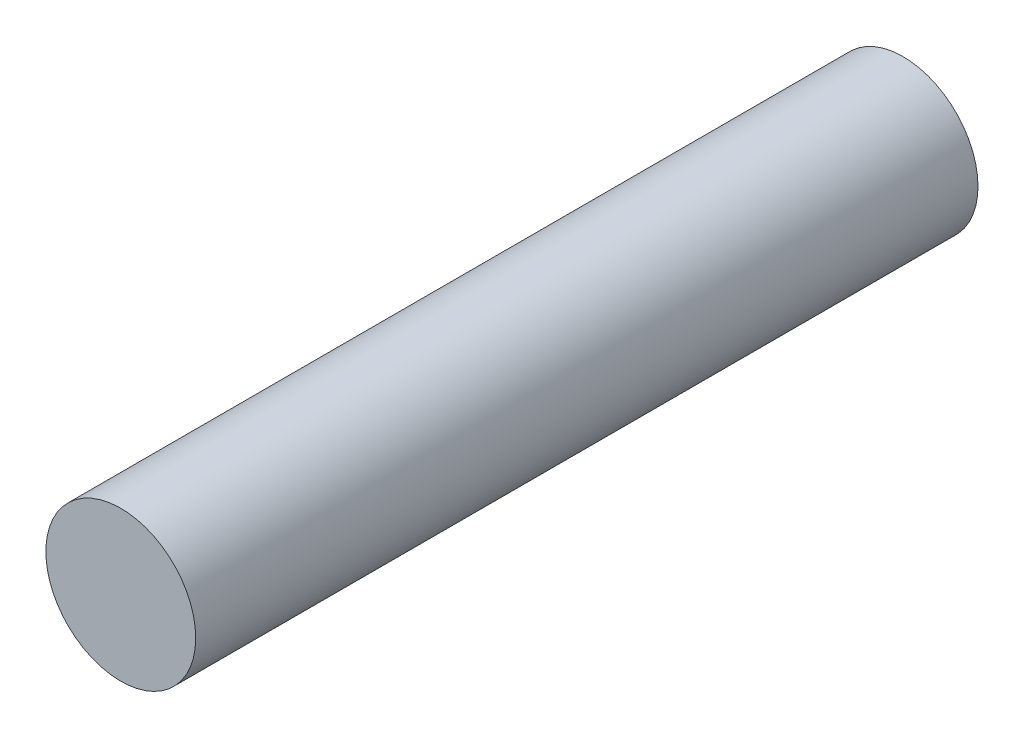
SolidWorks part; units mm, degrees
ref_plane "Front Plane" through (0, 0, 0) normal (0, 0, 1) x (1, 0, 0)
ref_plane "Top Plane" through (0, 0, 0) normal (0, 1, 0) x (1, 0, 0)
ref_plane "Right Plane" through (0, 0, 0) normal (1, 0, 0) x (0, 0, -1)
sketch "Sketch1" plane through (0, 0, 0) normal (0, 0, 1) x (1, 0, 0)
  circle A0 centre (0, 0) radius 1.5811
  dimension "D1" = 3.1623
extrude "Boss-Extrude1" add sketch "Sketch1" along normal blind 16.51
